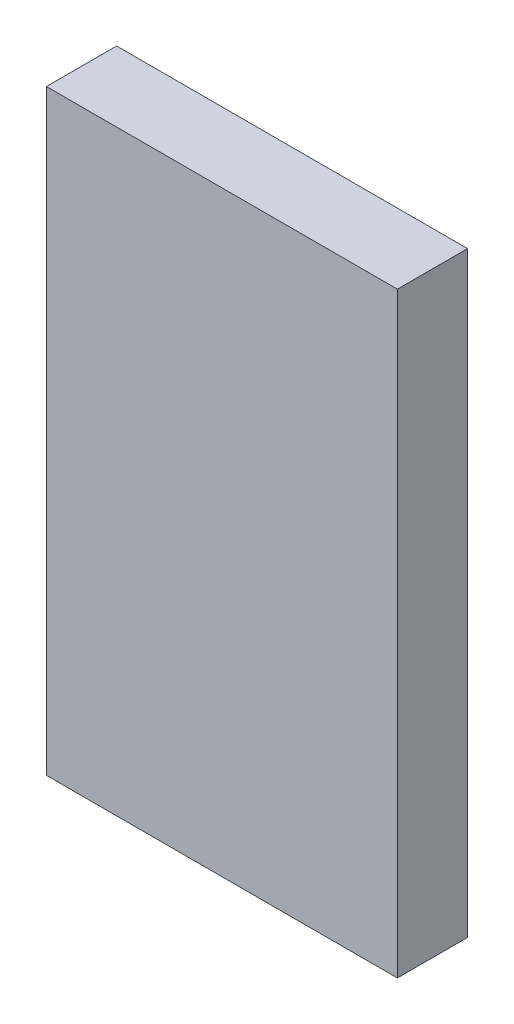
SolidWorks part; units mm, degrees
material "Silicon Rubber"
ref_plane "Front Plane" through (0, 0, 0) normal (0, 0, 1) x (1, 0, 0)
ref_plane "Top Plane" through (0, 0, 0) normal (0, 1, 0) x (1, 0, 0)
ref_plane "Right Plane" through (0, 0, 0) normal (1, 0, 0) x (0, 0, -1)
sketch "Sketch1" plane through (0, 0, 0) normal (0, 0, 1) x (1, 0, 0)
  line L0 (0, 0) -> (0, 34)
  line L1 (0, 34) -> (20, 34)
  line L2 (20, 34) -> (20, 0)
  line L3 (20, 0) -> (0, 0)
  dimension "D1" = 20
  dimension "D2" = 34
extrude "Joint Body" add sketch "Sketch1" along normal blind 4
equation "\"D1@Sketch1\"  = \"Wjoint@Parameters@RobotHandParameters.SLDPRT\""
equation "\"D2@Sketch1\"  = \"Ljointd@Parameters@RobotHandParameters.SLDPRT\" + 24"
equation "\"D1@Joint Body\" = \"Tjointd@Parameters@RobotHandParameters.SLDPRT\""
